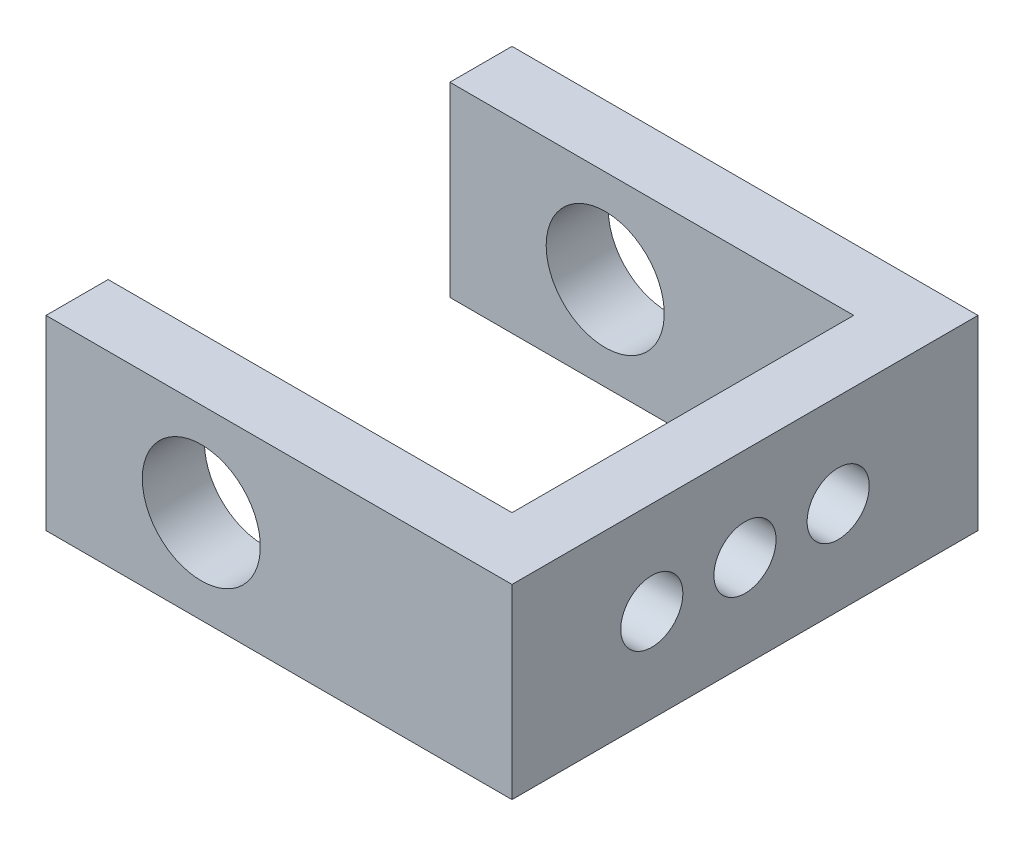
SolidWorks part; units mm, degrees
ref_plane "Front Plane" through (0, 0, 0) normal (0, 0, 1) x (1, 0, 0)
ref_plane "Top Plane" through (0, 0, 0) normal (0, 1, 0) x (1, 0, 0)
ref_plane "Right Plane" through (0, 0, 0) normal (1, 0, 0) x (0, 0, -1)
sketch "Sketch1" plane through (0, 0, 0) normal (0, 1, 0) x (1, 0, 0)
  line L0 (-55.7566, -25.749) -> (19.2434, -25.749)
  line L1 (19.2434, -25.749) -> (19.2434, 49.251)
  line L2 (19.2434, 49.251) -> (-55.7566, 49.251)
  line L3 (-55.7566, 49.251) -> (-55.7566, 39.251)
  line L4 (-55.7566, 39.251) -> (9.2434, 39.251)
  line L5 (9.2434, 39.251) -> (9.2434, -15.749)
  line L6 (9.2434, -15.749) -> (-55.7566, -15.749)
  line L7 (-55.7566, -15.749) -> (-55.7566, -25.749)
  dimension "D1" = 10
  dimension "D2" = 10
  dimension "D3" = 75
  dimension "D4" = 75
  dimension "D5" = 65
  dimension "D6" = 75
extrude "Boss-Extrude1" add sketch "Sketch1" along normal blind 30
ref_plane "Plane1" through (0, 0, -49.251) normal (0, 0, -1) x (-1, 0, 0)
sketch "Sketch3" plane through (0, 0, -49.251) normal (0, 0, -1) x (-1, 0, 0)
  line L0 (55.7566, 15) -> (30.7566, 15)
  line L1 (55.7566, 30) -> (55.7566, 0) construction
  circle A0 centre (30.7566, 15) radius 9.5
extrude "Cut-Extrude1" cut sketch "Sketch3" against normal blind 90
ref_plane "Plane2" through (19.2434, 0, 0) normal (1, 0, 0) x (0, 0, -1)
sketch "Sketch4" plane through (19.2434, 0, 0) normal (1, 0, 0) x (0, 0, -1)
  point P6 (11.751, 15)
  point P7 (26.751, 15)
  point P8 (-3.249, 15)
hole_wizard "M10x1.0 Tapped Hole1" positions "Sketch6" profile "Sketch5" tap size "M10x1.0" standard "ANSI Metric"
sketch "Sketch6" plane through (19.2434, 0, 0) normal (1, 0, 0) x (0, 0, -1)
  point P0 (-3.249, 15)
  point P3 (11.751, 15)
  point P6 (26.751, 15)
sketch "Sketch5" plane through (19.2434, 15, 3.249) normal (0, 1, 0) x (0, 0, -1)
  line L0 (0, 0) -> (0, 25.7039)
  line L1 (0, 25.7039) -> (4.5, 23)
  line L2 (4.5, 23) -> (4.5, 20)
  line L3 (4.5, 20) -> (5, 20)
  line L4 (5, 20) -> (5, 0)
  line L5 (5, 0) -> (0, 0)
  line L10 (0, 25.7039) -> (-4.5, 23) construction
  line L11 (0, -6.35) -> (0, 107.95) construction
  dimension "Tap Drill Dia." = 9
  dimension "Tap Drill Depth" = 23
  dimension "Thread Major Dia." = 10
  dimension "Thread Depth" = 20
  dimension "Drill Angle" = 118
